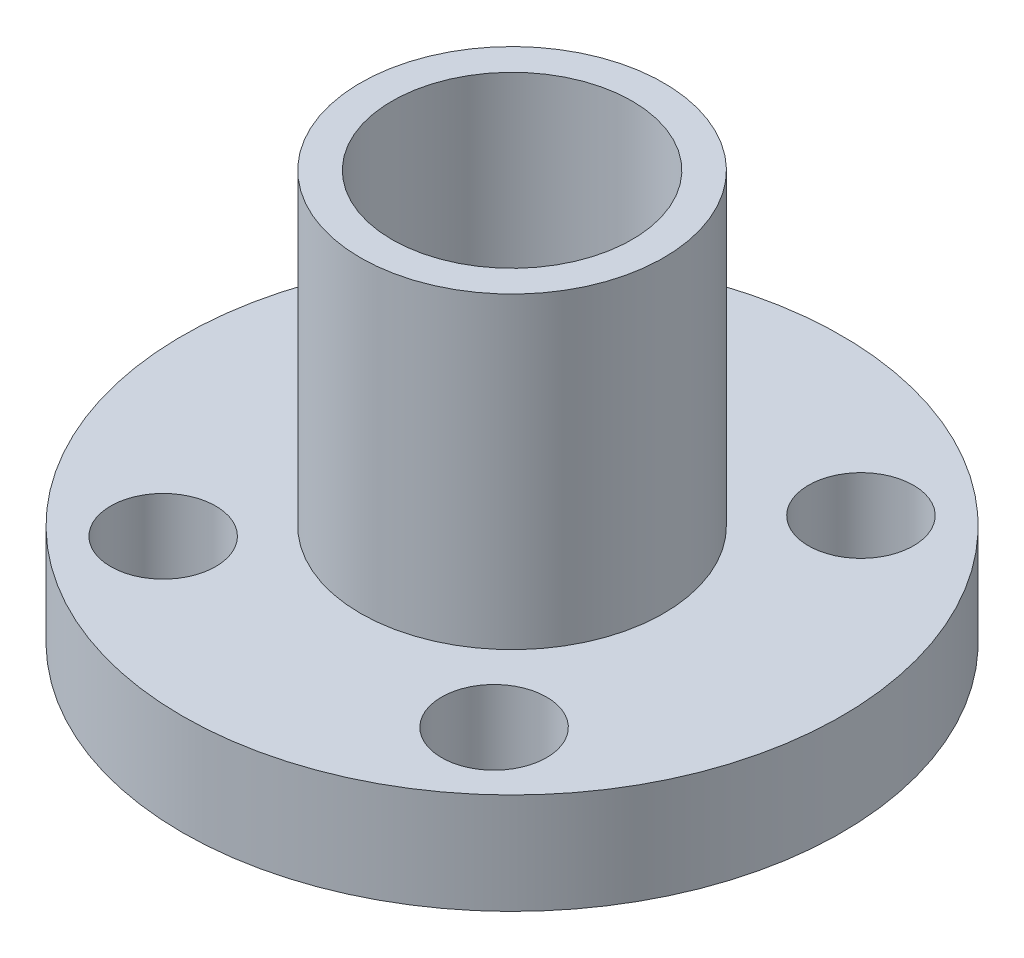
SolidWorks part; units mm, degrees
material "2.0966 (CuAl10Ni5Fe4)"
ref_plane "Alzado" through (0, 0, 0) normal (0, 0, 1) x (1, 0, 0)
ref_plane "Planta" through (0, 0, 0) normal (0, 1, 0) x (1, 0, 0)
ref_plane "Vista lateral" through (0, 0, 0) normal (1, 0, 0) x (0, 0, -1)
sketch "Croquis2" plane through (0, 0, 0) normal (0, 1, 0) x (1, 0, 0)
  circle A0 centre (0, 0) radius 10.98
  circle A1 centre (-5.5121, 6.1114) radius 1.75
  circle A2 centre (-5.5121, -6.1114) radius 1.75
  circle A3 centre (5.5121, -6.1114) radius 1.75
  circle A4 centre (5.5121, 6.1114) radius 1.75
  dimension "D1" = 21.96
extrude "Saliente-Extruir1" add sketch "Croquis2" along normal blind 3.36
sketch "Croquis3" plane through (0, 3.36, 0) normal (0, 1, 0) x (1, 0, 0)
  circle A0 centre (0, 0) radius 5.05
extrude "Saliente-Extruir2" add sketch "Croquis3" along normal blind 10.26
sketch "Croquis4" plane through (0, 0, 0) normal (0, -1, 0) x (1, 0, 0)
  circle A0 centre (0, 0) radius 5.05
extrude "Saliente-Extruir3" add sketch "Croquis4" along normal blind 1.38
sketch "Croquis5" plane through (0, 13.62, 0) normal (0, 1, 0) x (1, 0, 0)
  circle A0 centre (0, 0) radius 4
extrude "Cortar-Extruir1" cut sketch "Croquis5" against normal through all
